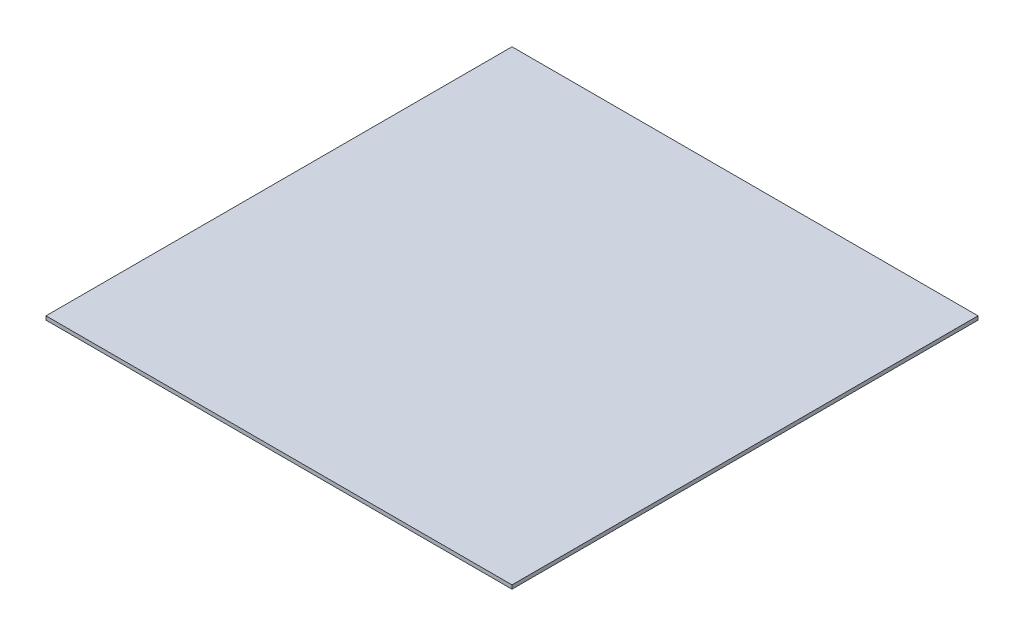
SolidWorks part; units mm, degrees
ref_plane "Front Plane" through (0, 0, 0) normal (0, 0, 1) x (1, 0, 0)
ref_plane "Top Plane" through (0, 0, 0) normal (0, 1, 0) x (1, 0, 0)
ref_plane "Right Plane" through (0, 0, 0) normal (1, 0, 0) x (0, 0, -1)
sketch "Sketch1" plane through (0, 0, 0) normal (0, 1, 0) x (1, 0, 0)
  line L1 (-185, -185) -> (185, -185)
  line L2 (-185, -185) -> (-185, 185)
  line L3 (-185, 185) -> (185, 185)
  line L4 (185, -185) -> (185, 185)
  line L5 (-185, -185) -> (185, 185) construction
  line L6 (-185, 185) -> (185, -185) construction
  point P0 (0, 0)
  dimension "D1" = 370
  dimension "D2" = 370
extrude "Boss-Extrude1" add sketch "Sketch1" along normal blind 3
